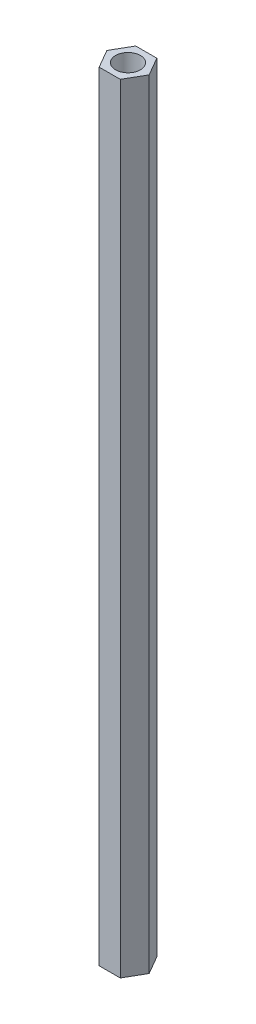
SolidWorks part; units mm, degrees
material "黄铜"
ref_plane "前视基准面" through (0, 0, 0) normal (0, 0, 1) x (1, 0, 0)
ref_plane "上视基准面" through (0, 0, 0) normal (0, 1, 0) x (1, 0, 0)
ref_plane "右视基准面" through (0, 0, 0) normal (1, 0, 0) x (0, 0, -1)
sketch "草图1" plane through (0, 0, 0) normal (0, 1, 0) x (1, 0, 0)
  line L1 (2.7135, 0) -> (1.3568, 2.35)
  line L2 (1.3568, 2.35) -> (-1.3568, 2.35)
  line L3 (-1.3568, 2.35) -> (-2.7135, 0)
  line L4 (-2.7135, 0) -> (-1.3568, -2.35)
  line L5 (-1.3568, -2.35) -> (1.3568, -2.35)
  line L6 (1.3568, -2.35) -> (2.7135, 0)
  circle A0 centre (0, 0) radius 2.35 construction
  dimension "D1" = 4.7
extrude "凸台-拉伸1" add sketch "草图1" along normal blind 100
sketch "草图2" plane through (0, 100, 0) normal (0, 1, 0) x (1, 0, 0)
  circle A0 centre (0, 0) radius 1.6
  dimension "D1" = 3.2
extrude "切除-拉伸1" cut sketch "草图2" against normal through all
